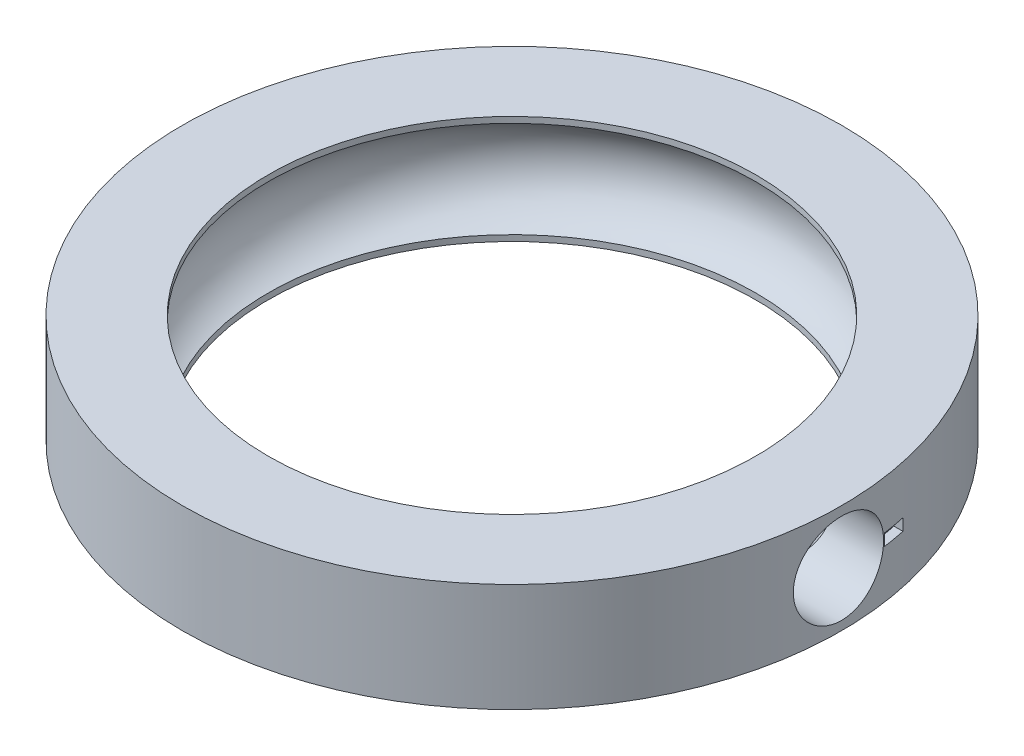
SolidWorks part; units mm, degrees
ref_plane "Front Plane" through (0, 0, 0) normal (0, 0, 1) x (1, 0, 0)
ref_plane "Top Plane" through (0, 0, 0) normal (0, 1, 0) x (1, 0, 0)
ref_plane "Right Plane" through (0, 0, 0) normal (1, 0, 0) x (0, 0, -1)
sketch "Sketch1" plane through (0, 0, 0) normal (0, 1, 0) x (1, 0, 0)
  circle A0 centre (0, 0) radius 18.25
  circle A1 centre (0, 0) radius 13.5
  dimension "D1" = 36.5
  dimension "D2" = 27
extrude "Boss-Extrude1" add sketch "Sketch1" along normal blind 6 contours A0 | A1
sketch "Sketch3" plane through (0, 0, 0) normal (0, 0, 1) x (1, 0, 0)
  line L1 (18.25, 6) -> (-18.25, 6) construction
  line L2 (0, 0) -> (0, 12.4992) construction
  line L4 (-13.5, 6) -> (-13.5, 17.212) construction
  circle A1 centre (-12.5, 3) radius 2.85
  dimension "D2" = 3
  dimension "D1" = 5.7
  dimension "D3" = 1
revolve "Cut-Revolve1" cut sketch "Sketch3" angle 360 about L2
sketch "Sketch4" plane through (0, 0, 0) normal (1, 0, 0) x (0, 0, -1)
  line L0 (-18.25, 0) -> (18.25, 0) construction
  circle A0 centre (0, 3) radius 2.5
  dimension "D1" = 5
  dimension "D2" = 3
extrude "Cut-Extrude1" cut sketch "Sketch4" against normal blind 10 and the other way through all
sketch "Sketch6" plane through (0, 0, 0) normal (1, 0, 0) x (0, 0, -1)
  line L1 (2.5566, 3.3258) -> (3.7969, 3.3258)
  line L2 (2.5566, 3.3258) -> (2.5566, 2.6742)
  line L3 (2.5566, 2.6742) -> (3.7969, 2.6742)
  line L4 (3.7969, 3.3258) -> (3.7969, 2.6742)
  line L5 (2.5566, 3.3258) -> (3.7969, 2.6742) construction
  line L6 (2.5566, 2.6742) -> (3.7969, 3.3258) construction
  point P0 (3.1767, 3)
extrude "Cut-Extrude2" cut sketch "Sketch6" against normal blind 0.5 from surface starting at face at (0, 6, 18.25)
